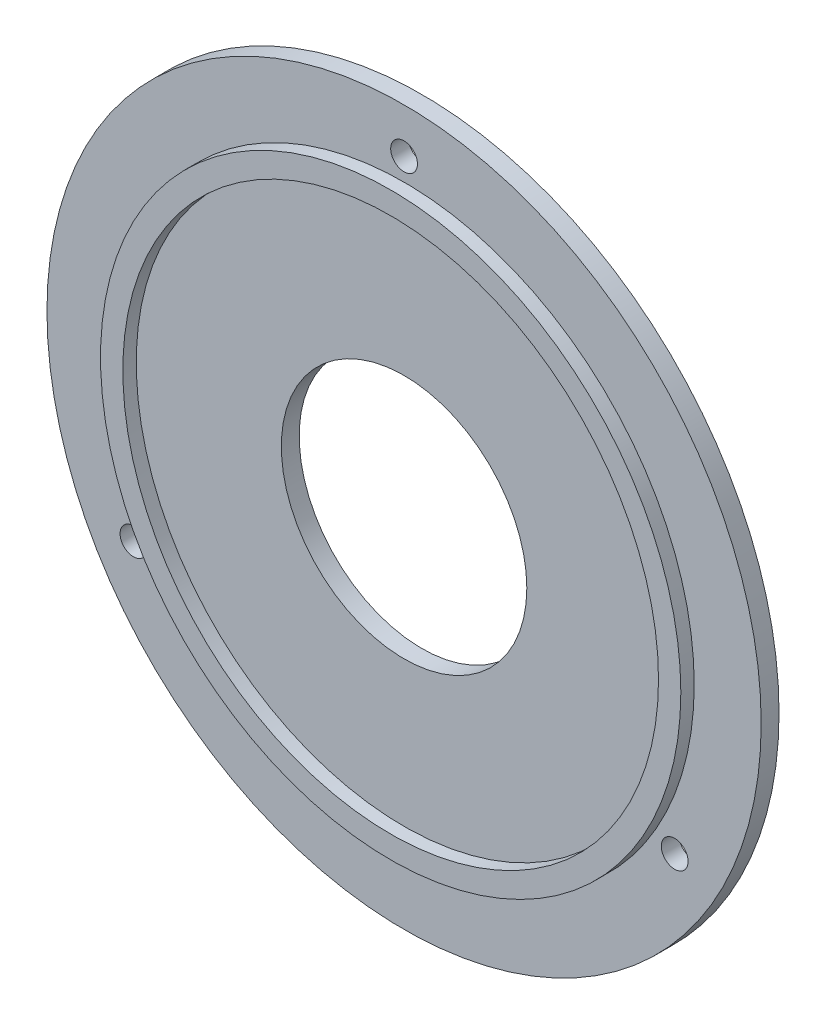
SolidWorks part; units mm, degrees
ref_plane "Front Plane" through (0, 0, 0) normal (0, 0, 1) x (1, 0, 0)
ref_plane "Top Plane" through (0, 0, 0) normal (0, 1, 0) x (1, 0, 0)
ref_plane "Right Plane" through (0, 0, 0) normal (1, 0, 0) x (0, 0, -1)
sketch "Sketch1" plane through (0, 0, 0) normal (0, 0, 1) x (1, 0, 0)
  circle A0 centre (0, 0) radius 80
extrude "Boss-Extrude1" add sketch "Sketch1" along normal blind 4
sketch "Sketch2" plane through (0, 0, 4) normal (0, 0, 1) x (1, 0, 0)
  circle A0 centre (0, 0) radius 65
  circle A1 centre (0, 0) radius 60
extrude "Boss-Extrude2" add sketch "Sketch2" along normal blind 3
sketch "Sketch3" plane through (0, 0, 0) normal (0, 0, -1) x (-1, 0, 0)
  circle A0 centre (0, 0) radius 70
  circle A1 centre (0, 70) radius 3
  circle A2 centre (60.6218, -35) radius 3
  circle A3 centre (-60.6218, -35) radius 3
  point P11 (0, 0)
  dimension "D1" = 3
extrude "Cut-Extrude2" cut sketch "Sketch3" against normal through all contours A1 | A3 | A2
sketch "Sketch5" plane through (0, 0, 0) normal (0, 0, 1) x (1, 0, 0)
  circle A0 centre (0, 0) radius 27.5
extrude "Cut-Extrude4" cut sketch "Sketch5" along normal through all
